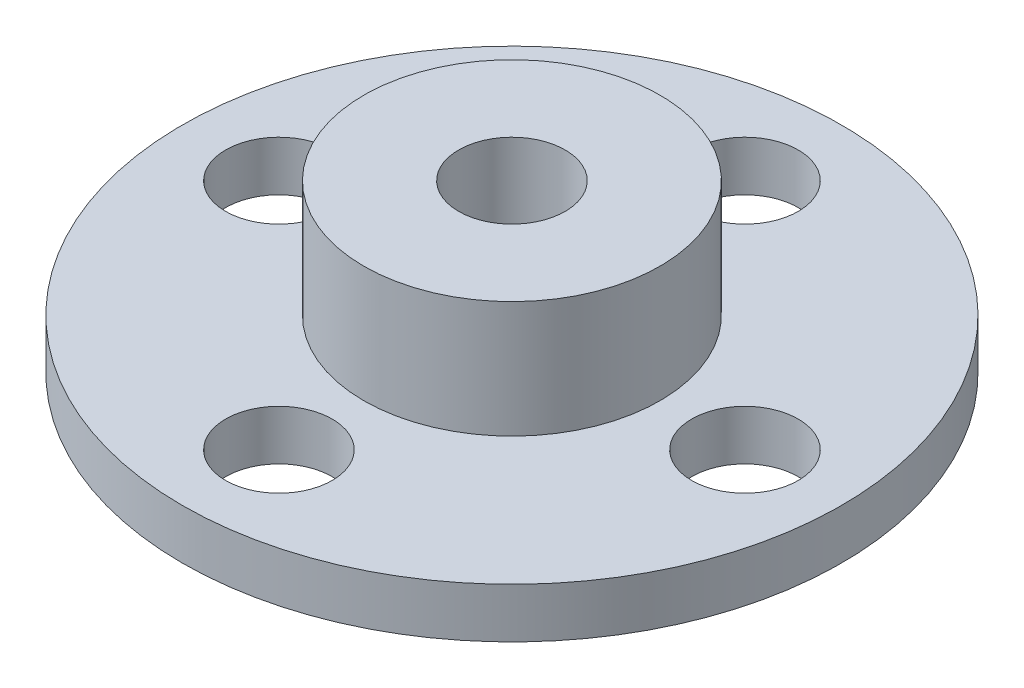
SolidWorks part; units mm, degrees
material "6061 Alloy"
ref_plane "Front Plane" through (0, 0, 0) normal (0, 0, 1) x (1, 0, 0)
ref_plane "Top Plane" through (0, 0, 0) normal (0, 1, 0) x (1, 0, 0)
ref_plane "Right Plane" through (0, 0, 0) normal (1, 0, 0) x (0, 0, -1)
sketch "Sketch1" plane through (0, 0, 0) normal (0, 1, 0) x (1, 0, 0)
  line L1 (-7, 7) -> (7, 7) construction
  line L2 (-7, 7) -> (-7, -7) construction
  line L3 (-7, -7) -> (7, -7) construction
  line L4 (7, 7) -> (7, -7) construction
  circle A0 centre (0, 0) radius 9.9
  circle A1 centre (0, 0) radius 1.6
  circle A2 centre (0, 0) radius 7 construction
  circle A3 centre (0, 7) radius 1.6
  circle A4 centre (7, 0) radius 1.6
  circle A5 centre (0, -7) radius 1.6
  circle A6 centre (-7, 0) radius 1.6
  dimension "D8" = 3.2
  dimension "D9" = 3.2
  dimension "D10" = 3.2
  dimension "D11" = 3.2
  dimension "D2" = 3.2
  dimension "D3" = 14
  dimension "D12" = 19.8
  dimension "D4" = 0
  dimension "D5" = 0
  dimension "D6" = 0
  dimension "D7" = 0
extrude "Boss-Extrude1" add sketch "Sketch1" along normal blind 1.5
sketch "Sketch2" plane through (0, 1.5, 0) normal (0, 1, 0) x (1, 0, 0)
  circle A0 centre (0, 0) radius 4.45
  circle A1 centre (0, 0) radius 1.6
  dimension "D1" = 8.9
  dimension "D2" = 3.2
extrude "Boss-Extrude3" add sketch "Sketch2" along normal blind 3.5
